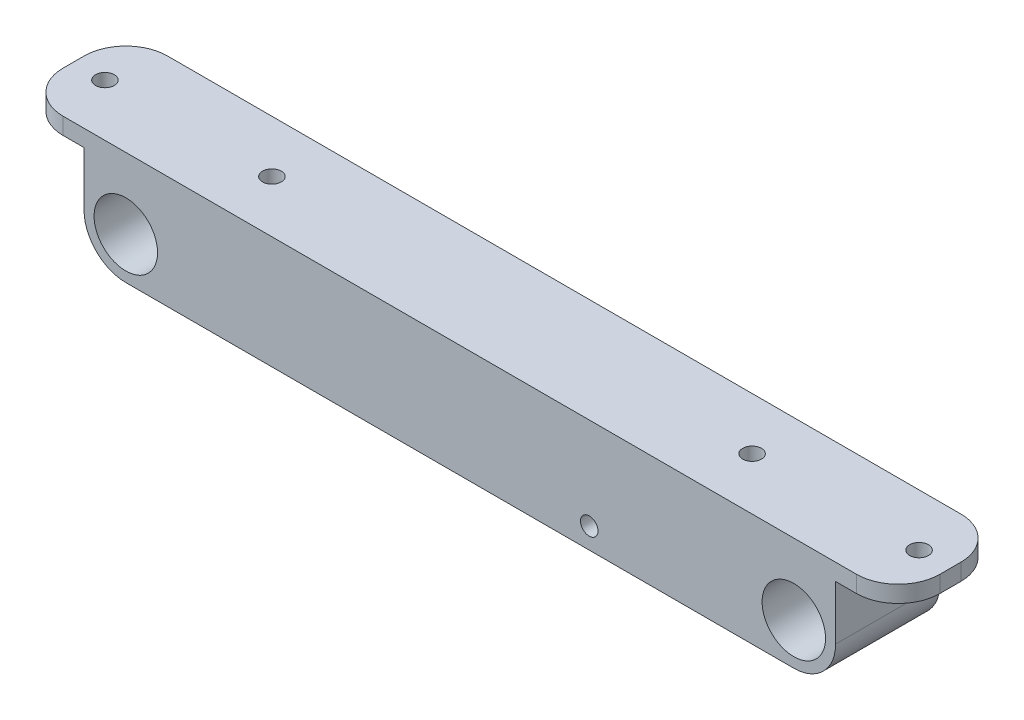
SolidWorks part; units mm, degrees
ref_plane "Front Plane" through (0, 0, 0) normal (0, 0, 1) x (1, 0, 0)
ref_plane "Top Plane" through (0, 0, 0) normal (0, 1, 0) x (1, 0, 0)
ref_plane "Right Plane" through (0, 0, 0) normal (1, 0, 0) x (0, 0, -1)
sketch "Sketch1" plane through (0, 0, 0) normal (0, 0, 1) x (1, 0, 0)
  line L0 (-80, 0) -> (0, 0) construction
  line L1 (0, 0) -> (80, 0) construction
  line L2 (-90, 0) -> (-90, 17)
  line L3 (-90, 17) -> (90, 17)
  line L4 (90, 17) -> (90, 0)
  line L5 (-70, 0) -> (-70, 13)
  line L6 (-70, 13) -> (70, 13)
  line L7 (70, 13) -> (70, 0)
  circle A0 centre (-80, 0) radius 7.6
  circle A1 centre (80, 0) radius 7.6
  arc A2 (-90, 0) -> (-70, 0) centre (-80, 0) ccw
  arc A3 (70, 0) -> (90, 0) centre (80, 0) ccw
  dimension "D2" = 15.2
  dimension "D3" = 20
  dimension "D1" = 80
  dimension "D4" = 17
  dimension "D5" = 4
extrude "Boss-Extrude1" add sketch "Sketch1" along normal blind 25
sketch "Sketch2" plane through (0, 0, 0) normal (0, 0, -1) x (-1, 0, 0)
  line L0 (-90, 17) -> (90, 17) construction
  line L1 (-16, 17) -> (-46, 17)
  line L2 (-16, 17) -> (-16, -10)
  line L3 (-16, -10) -> (-46, -10)
  line L4 (-46, 17) -> (-46, -10)
  line L5 (70, 13) -> (-70, 13) construction
  point P8 (-31, -10)
  point P9 (0, 13)
  dimension "D1" = 23
  dimension "D2" = 31
  dimension "D3" = 30
extrude "Boss-Extrude2" add sketch "Sketch2" against normal up to surface (25 mm away) up to face at (-72.4, 0, 25)
sketch "Sketch3" plane through (0, 0, 0) normal (0, 0, -1) x (-1, 0, 0)
  line L0 (80, -10) -> (-12, -10)
  line L1 (-42, -10) -> (-80, -10)
  line L2 (-12, -10) -> (-42, -10)
  line L10 (90, 0) -> (90, 17)
  line L11 (90, 17) -> (-90, 17)
  line L12 (-90, 17) -> (-90, 0)
  line L13 (-70, 0) -> (-70, 13)
  line L14 (-70, 13) -> (-46, 13)
  line L15 (-46, 13) -> (-46, -10)
  line L16 (-46, -10) -> (-16, -10)
  line L17 (-16, -10) -> (-16, 13)
  line L18 (-16, 13) -> (70, 13)
  line L19 (70, 13) -> (70, 0)
  line L20 (90, 0) -> (90, 17)
  line L21 (90, 17) -> (-90, 17)
  line L22 (-90, 17) -> (-90, 0)
  circle A0 centre (80, 0) radius 7.6
  circle A1 centre (-80, 0) radius 7.6
  arc A2 (-90, 0) -> (-70, 0) centre (-80, 0) ccw
  arc A3 (70, 0) -> (90, 0) centre (80, 0) ccw
  arc A4 (-90, 0) -> (-80, -10) centre (-80, 0) ccw
  arc A5 (80, -10) -> (90, 0) centre (80, 0) ccw
  dimension "D1" = 0
extrude "Boss-Extrude3" add sketch "Sketch3" against normal blind 2
ref_plane "Plane1" through (0, 0, 12.5) normal (0, 0, 1) x (1, 0, 0)
mirror "Mirror1" about plane through (0, 0, 12.5) normal (0, 0, 1) of "Boss-Extrude3"
chamfer "Chamfer1" distance 5 angle 45 2 edges at (-70, 13, 12.5) (70, 13, 12.5)
sketch "Sketch5" plane through (-90, 0, 0) normal (-1, 0, 0) x (0, 0, 1)
  line L0 (25, 17) -> (25, 0) construction
  line L1 (0, 17) -> (25, 17)
  line L2 (0, 17) -> (0, 13)
  line L3 (0, 13) -> (25, 13)
  line L4 (25, 17) -> (25, 13)
  dimension "D1" = 4
extrude "Boss-Extrude4" add sketch "Sketch5" along normal blind 15
sketch "Sketch6" plane through (0, 13, 0) normal (0, -1, 0) x (-1, 0, 0)
  line L0 (90, -25) -> (105, 0) construction
  circle A0 centre (97.5, -12.5) radius 2.25
  dimension "D1" = 4.5
extrude "Cut-Extrude2" cut sketch "Sketch6" against normal blind 15
fillet "Fillet1" radius 10 2 edges at (-105, 15, 0) (-105, 15, 25)
mirror "Mirror2" about plane through (0, 0, 0) normal (1, 0, 0) of "Fillet1", "Boss-Extrude4"
mirror "Mirror4" about plane through (0, 0, 0) normal (1, 0, 0) of "Cut-Extrude2"
sketch "Sketch7" plane through (0, 17, 0) normal (0, 1, 0) x (1, 0, 0)
  circle A0 centre (-57.5, -12.5) radius 2.25
  circle A1 centre (57.5, -12.5) radius 2.25
  circle A2 centre (-97.5, -12.5) radius 2.25 construction
  circle A3 centre (97.5, -12.5) radius 2.25 construction
  dimension "D1" = 40
  dimension "D2" = 40
extrude "Cut-Extrude3" cut sketch "Sketch7" against normal blind 15
sketch "Sketch8" plane through (0, -10, 0) normal (0, -1, 0) x (1, 0, 0)
  line L0 (20, 19) -> (20, 6)
  line L1 (16, 23) -> (46, 23)
  line L2 (16, 23) -> (16, 2)
  line L3 (16, 2) -> (46, 2)
  line L4 (46, 23) -> (46, 2)
  line L5 (20, 6) -> (42, 6)
  line L6 (42, 19) -> (42, 6)
  line L7 (20, 19) -> (42, 19)
  circle A0 centre (20, 19) radius 1.95
  circle A1 centre (42, 19) radius 1.95
  circle A2 centre (42, 6) radius 1.95
  circle A3 centre (20, 6) radius 1.95
  dimension "D2" = 3.9
  dimension "D1" = 4
extrude "Cut-Extrude4" cut sketch "Sketch8" against normal blind 15 contours L7 A0 L0 | L0 A0 L7 | L7 A1 L6 | L6 A1 L7 | L5 A2 L6 | L6 A2 L5 | L5 A3 L0 | L0 A3 L5
sketch "Sketch9" plane through (0, 0, 25) normal (0, 0, 1) x (1, 0, 0)
  line L0 (80, -10) -> (-80, -10) construction
  circle A0 centre (31, -5) radius 2.1
  dimension "D1" = 4.2
  dimension "D2" = 15
  dimension "D3" = 5
extrude "Cut-Extrude5" cut sketch "Sketch9" against normal blind 28.4681
sketch "Sketch10" plane through (0, 0, 0) normal (0, 0, -1) x (-1, 0, 0)
  line L1 (-26.6699, -5) -> (-28.8349, -1.25)
  line L2 (-28.8349, -1.25) -> (-33.1651, -1.25)
  line L3 (-33.1651, -1.25) -> (-35.3301, -5)
  line L4 (-35.3301, -5) -> (-33.1651, -8.75)
  line L5 (-33.1651, -8.75) -> (-28.8349, -8.75)
  line L6 (-28.8349, -8.75) -> (-26.6699, -5)
  circle A0 centre (-31, -5) radius 3.75 construction
  dimension "D1" = 7.5
extrude "Cut-Extrude6" cut sketch "Sketch10" against normal blind 5
